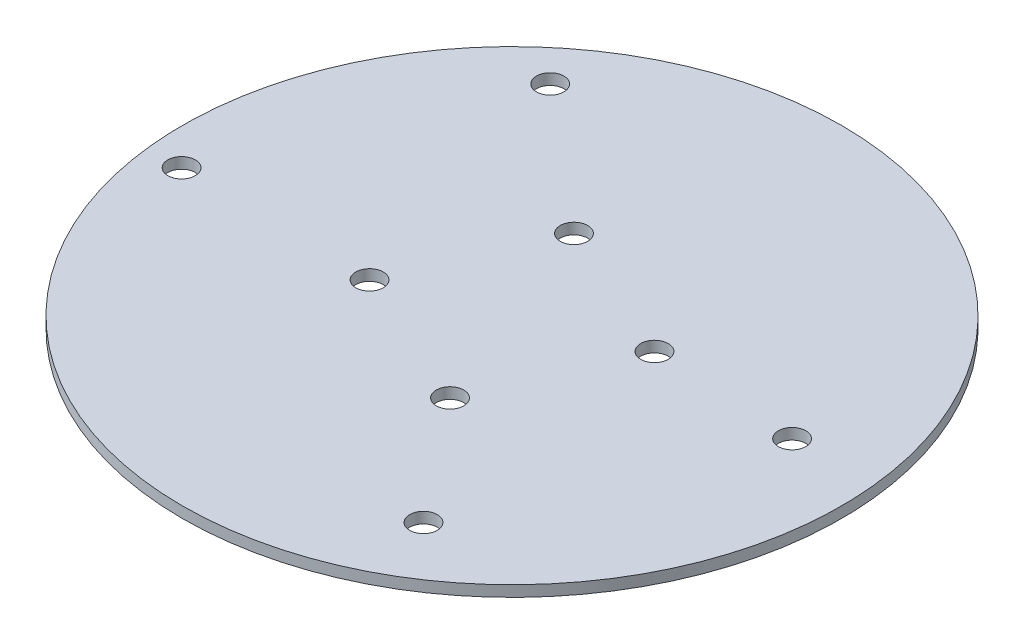
SolidWorks part; units mm, degrees
material "6061-T6 (SS)"
ref_plane "Front Plane" through (0, 0, 0) normal (0, 0, 1) x (1, 0, 0)
ref_plane "Top Plane" through (0, 0, 0) normal (0, 1, 0) x (1, 0, 0)
ref_plane "Right Plane" through (0, 0, 0) normal (1, 0, 0) x (0, 0, -1)
sketch "Sketch1" plane through (0, 0, 0) normal (0, 1, 0) x (1, 0, 0)
  circle A17 centre (0, 0) radius 76.2
  dimension "D1" = 152.4
extrude "Boss-Extrude1" add sketch "Sketch1" along normal blind 2.54
sketch "Sketch2" plane through (0, 0, 0) normal (0, -1, 0) x (1, 0, 0)
  circle A0 centre (-67.8141, 8.5853) radius 3.175
  circle A1 centre (-41.9798, -50.8095) radius 3.175
  circle A2 centre (57.0116, -7.7524) radius 3.175
  circle A3 centre (31.1773, 51.6424) radius 3.175
  dimension "D1" = 6.35
extrude "Cut-Extrude1" cut sketch "Sketch2" against normal blind 2.54
sketch "Sketch4" plane through (0, 2.54, 0) normal (0, 1, 0) x (1, 0, 0)
  circle A0 centre (-9.3062, 23.6337) radius 3.175
  circle A1 centre (23.6337, 9.3062) radius 3.175
  circle A2 centre (9.3062, -23.6337) radius 3.175
  circle A3 centre (-23.6337, -9.3062) radius 3.175
  dimension "D1" = 6.35
extrude "Cut-Extrude3" cut sketch "Sketch4" against normal through all
equation "\"Rocket Diameter\"= 12in"
equation "\"Rocket Thickness\"= .25in"
equation "\"Plate_Mount\"= \"Rocket Diameter\" - 6 * \"Rocket Thickness\""
